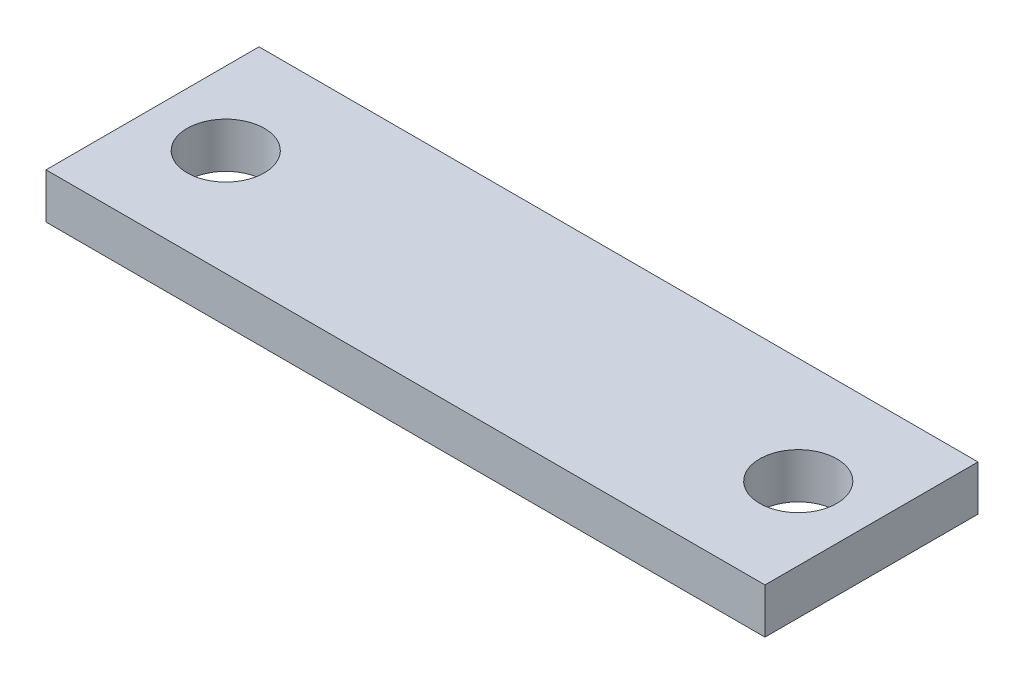
SolidWorks part; units mm, degrees
ref_plane "Front Plane" through (0, 0, 0) normal (0, 0, 1) x (1, 0, 0)
ref_plane "Top Plane" through (0, 0, 0) normal (0, 1, 0) x (1, 0, 0)
ref_plane "Right Plane" through (0, 0, 0) normal (1, 0, 0) x (0, 0, -1)
sketch "Sketch1" plane through (0, 0, 0) normal (0, 1, 0) x (1, 0, 0)
  line L0 (-30.4, 0) -> (43, 0) construction
  line L1 (0, -43.8) -> (0, 29.6) construction
  line L3 (-13.5, 4) -> (13.5, 4)
  line L4 (-13.5, 4) -> (-13.5, -4)
  line L5 (-13.5, -4) -> (13.5, -4)
  line L6 (13.5, 4) -> (13.5, -4)
  circle A0 centre (-10.75, 0) radius 1.45
  circle A1 centre (10.75, 0) radius 1.45
  dimension "D3" = 2.9
  dimension "D1" = 8
  dimension "D2" = 27
  dimension "D4" = 21.5
extrude "Boss-Extrude1" add sketch "Sketch1" along normal blind 1.7
